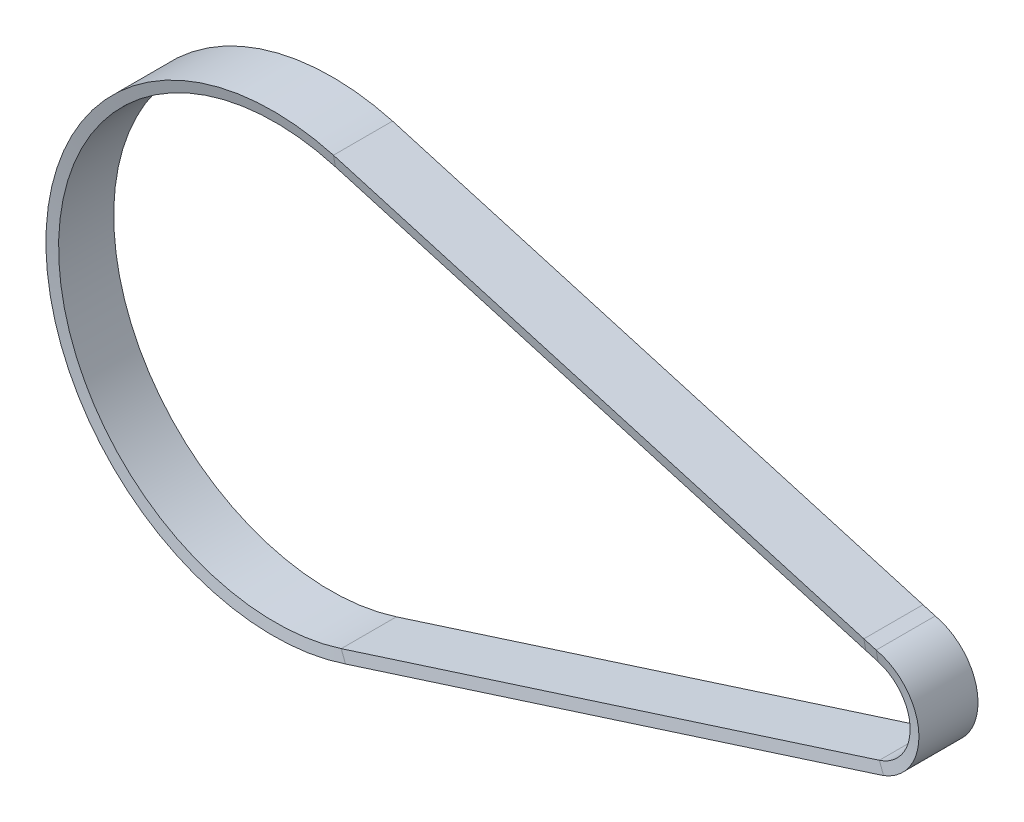
SolidWorks part; units mm, degrees
ref_plane "Front Plane" through (0, 0, 0) normal (0, 0, 1) x (1, 0, 0)
ref_plane "Top Plane" through (0, 0, 0) normal (0, 1, 0) x (1, 0, 0)
ref_plane "Right Plane" through (0, 0, 0) normal (1, 0, 0) x (0, 0, -1)
sketch "Sketch1" plane through (0, 0, 0) normal (0, 0, 1) x (1, 0, 0)
  line L0 (-269.3678, 101.4446) -> (6.2596, 21.6117)
  line L1 (-266.4127, -108.969) -> (6.8641, -21.4274)
  line L2 (-299.9704, -4.2127) -> (0, 0) construction
  arc A0 (6.8641, -21.4274) -> (6.2596, 21.6117) centre (0, 0) ccw
  arc A1 (-269.3678, 101.4446) -> (-266.4127, -108.969) centre (-299.9704, -4.2127) ccw
  dimension "D1" = 45
  dimension "D2" = 220
  dimension "D3" = 300
sketch "Sketch2" plane through (0, 0, 0) normal (1, 0, 0) x (0, 0, -1)
  line L0 (-15, 29.0648) -> (15, 29.0648)
  line L1 (15, 29.0648) -> (14, 23.4248)
  line L2 (14, 23.4248) -> (-14, 23.4248)
  line L3 (-14, 23.4248) -> (-15, 29.0648)
  line L4 (0, 29.0648) -> (0, 23.4248) construction
  line L5 (0, 101.4446) -> (0, 21.6117) construction
  dimension "D1" = 30
  dimension "D2" = 28
  dimension "D3" = 5.64
sweep "Sweep1" add profiles "Sketch2" path "Sketch1"
